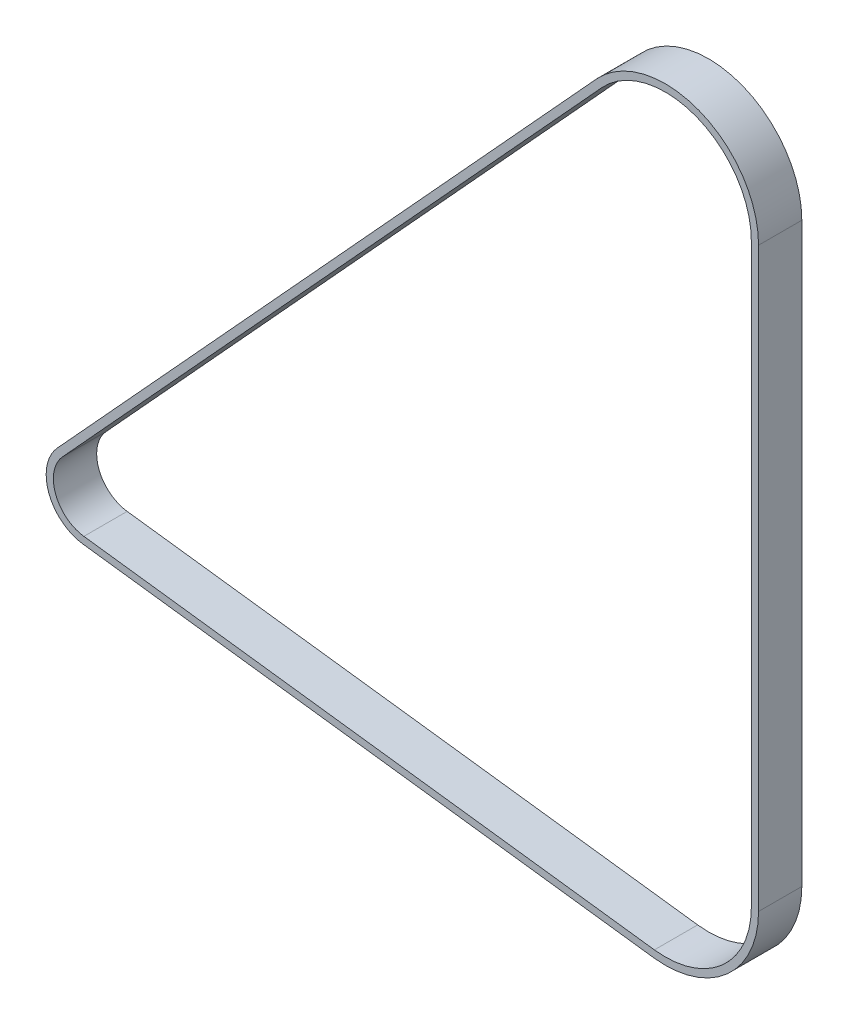
SolidWorks part; units mm, degrees
ref_plane "Front Plane" through (0, 0, 0) normal (0, 0, 1) x (1, 0, 0)
ref_plane "Top Plane" through (0, 0, 0) normal (0, 1, 0) x (1, 0, 0)
ref_plane "Right Plane" through (0, 0, 0) normal (1, 0, 0) x (0, 0, -1)
sketch "Sketch2" plane through (0, 0, 0) normal (0, 0, 1) x (1, 0, 0)
  line L0 (0, 0) -> (1, 0) construction
  line L1 (0, 0) -> (0, 1) construction
  line L2 (-0.9743, -7.6277) -> (124.6002, -23.667)
  line L3 (145.9411, -4.8786) -> (145.9411, 122.1214)
  line L4 (113.0263, 134.9082) -> (-5.673, 5.1911)
  arc A0 (-5.673, 5.1911) -> (-0.9743, -7.6277) centre (0, 0) ccw
  arc A1 (124.6002, -23.667) -> (145.9411, -4.8786) centre (127, -4.8786) ccw
  arc A2 (145.9411, 122.1214) -> (113.0263, 134.9082) centre (127, 122.1214) ccw
extrude "Extrude-Thin1" add sketch "Sketch2" along normal mid plane 9.525 thin
